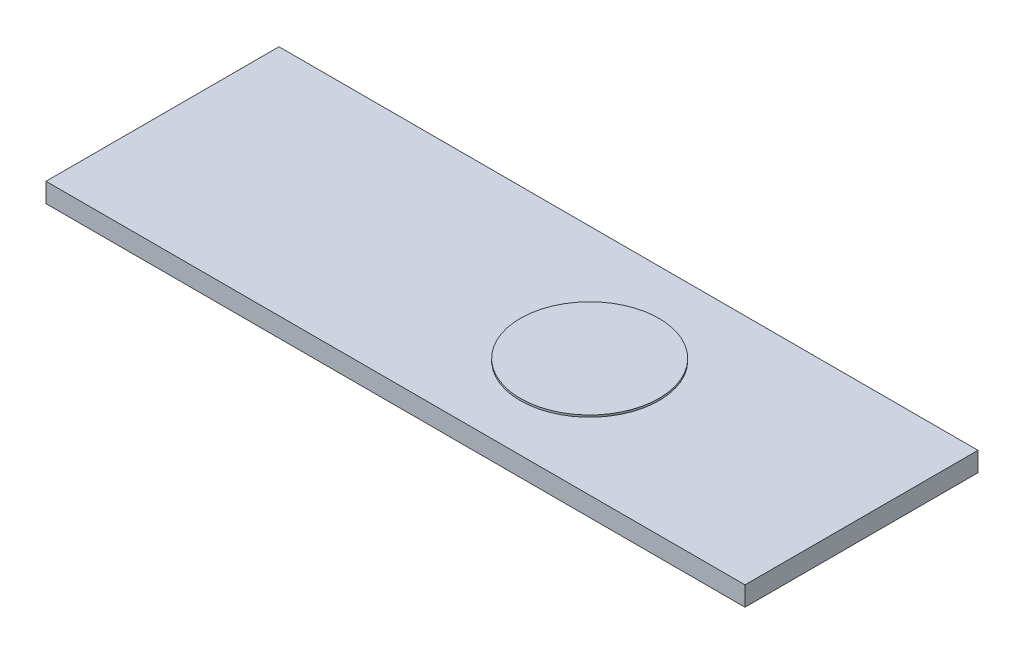
SolidWorks part; units mm, degrees
ref_plane "Front Plane" through (0, 0, 0) normal (0, 0, 1) x (1, 0, 0)
ref_plane "Top Plane" through (0, 0, 0) normal (0, 1, 0) x (1, 0, 0)
ref_plane "Right Plane" through (0, 0, 0) normal (1, 0, 0) x (0, 0, -1)
sketch "Sketch1" plane through (0, 0, 0) normal (0, 1, 0) x (1, 0, 0)
  line L1 (18, -6) -> (-18, -6)
  line L2 (18, -6) -> (18, 6)
  line L3 (18, 6) -> (-18, 6)
  line L4 (-18, -6) -> (-18, 6)
  line L5 (18, -6) -> (-18, 6) construction
  line L6 (18, 6) -> (-18, -6) construction
  point P0 (0, 0)
  dimension "D1" = 12
  dimension "D2" = 36
extrude "SPE" add sketch "Sketch1" along normal blind 1
sketch "Sketch2" plane through (0, 1, 0) normal (0, 1, 0) x (1, 0, 0)
  line L0 (18, -6) -> (18, 6) construction
  circle A0 centre (4, 0) radius 3.5719
  dimension "D1" = 14
extrude "WE" add sketch "Sketch2" along normal blind 0.1
